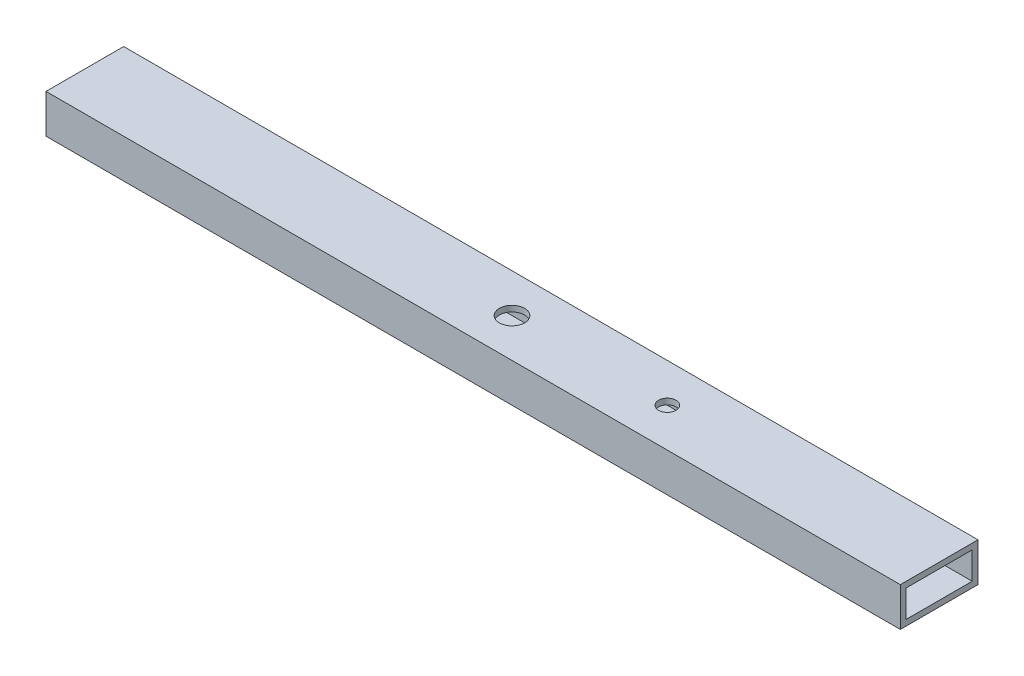
SolidWorks part; units mm, degrees
ref_plane "Front Plane" through (0, 0, 0) normal (0, 0, 1) x (1, 0, 0)
ref_plane "Top Plane" through (0, 0, 0) normal (0, 1, 0) x (1, 0, 0)
ref_plane "Right Plane" through (0, 0, 0) normal (1, 0, 0) x (0, 0, -1)
sketch "Sketch1" plane through (0, 0, 0) normal (1, 0, 0) x (0, 0, -1)
  line L0 (-8.5, 3.5) -> (8.5, 3.5)
  line L1 (-10, 5) -> (10, 5)
  line L2 (-10, 5) -> (-10, -5)
  line L3 (-10, -5) -> (10, -5)
  line L4 (10, 5) -> (10, -5)
  line L5 (-10, 5) -> (10, -5) construction
  line L6 (-10, -5) -> (10, 5) construction
  line L7 (8.5, 3.5) -> (8.5, -3.5)
  line L8 (-8.5, -3.5) -> (8.5, -3.5)
  line L9 (-8.5, 3.5) -> (-8.5, -3.5)
  point P0 (0, 0)
  dimension "D1" = 20
  dimension "D2" = 10
  dimension "D3" = 1.5
extrude "Boss-Extrude1" add sketch "Sketch1" along normal blind 220
sketch "Sketch2" plane through (0, 5, 0) normal (0, 1, 0) x (1, 0, 0)
  line L0 (0, 0) -> (220, 0) construction
  line L1 (220, 10) -> (220, -10) construction
  circle A0 centre (110, 0) radius 3.25
  circle A1 centre (150, 0) radius 2.25
  dimension "D1" = 6.5
  dimension "D2" = 4.5
  dimension "D3" = 40
extrude "Cut-Extrude1" cut sketch "Sketch2" against normal through all
